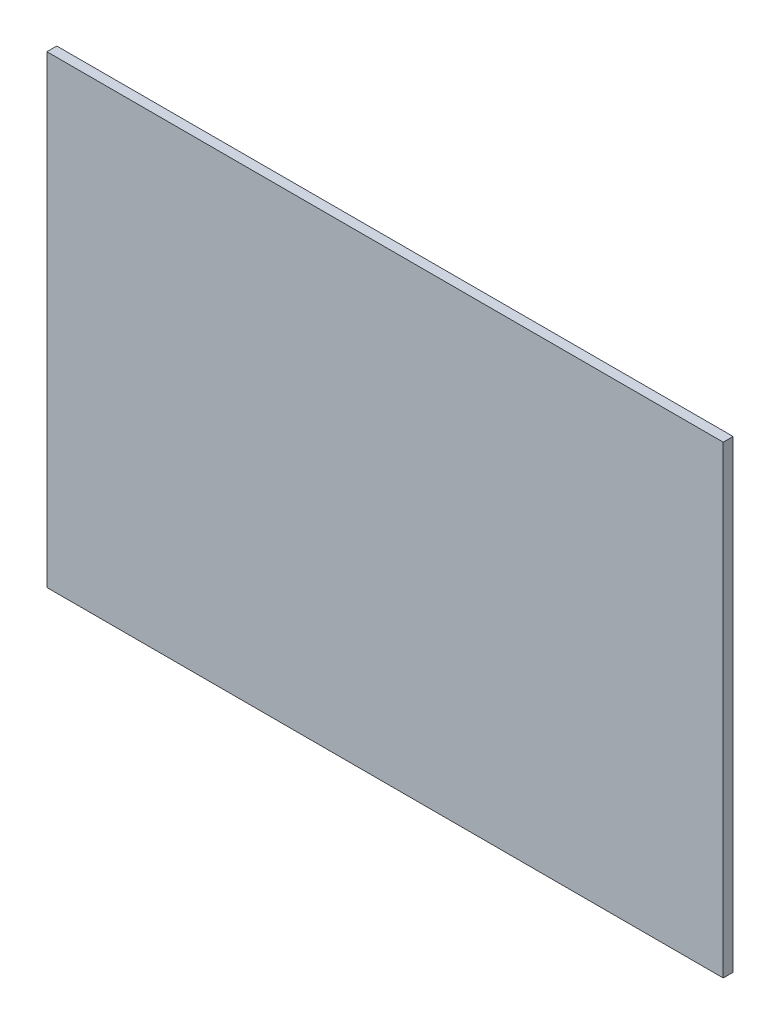
SolidWorks part; units mm, degrees
ref_plane "Front Plane" through (0, 0, 0) normal (0, 0, 1) x (1, 0, 0)
ref_plane "Top Plane" through (0, 0, 0) normal (0, 1, 0) x (1, 0, 0)
ref_plane "Right Plane" through (0, 0, 0) normal (1, 0, 0) x (0, 0, -1)
sketch "Sketch1" plane through (0, 0, 0) normal (0, 0, 1) x (1, 0, 0)
  line L1 (-138.2143, 104.1964) -> (135.7857, 104.1964)
  line L2 (-138.2143, 104.1964) -> (-138.2143, -83.8036)
  line L3 (-138.2143, -83.8036) -> (135.7857, -83.8036)
  line L4 (135.7857, 104.1964) -> (135.7857, -83.8036)
  dimension "D1" = 188
  dimension "D2" = 274
extrude "Boss-Extrude1" add sketch "Sketch1" along normal blind 4
